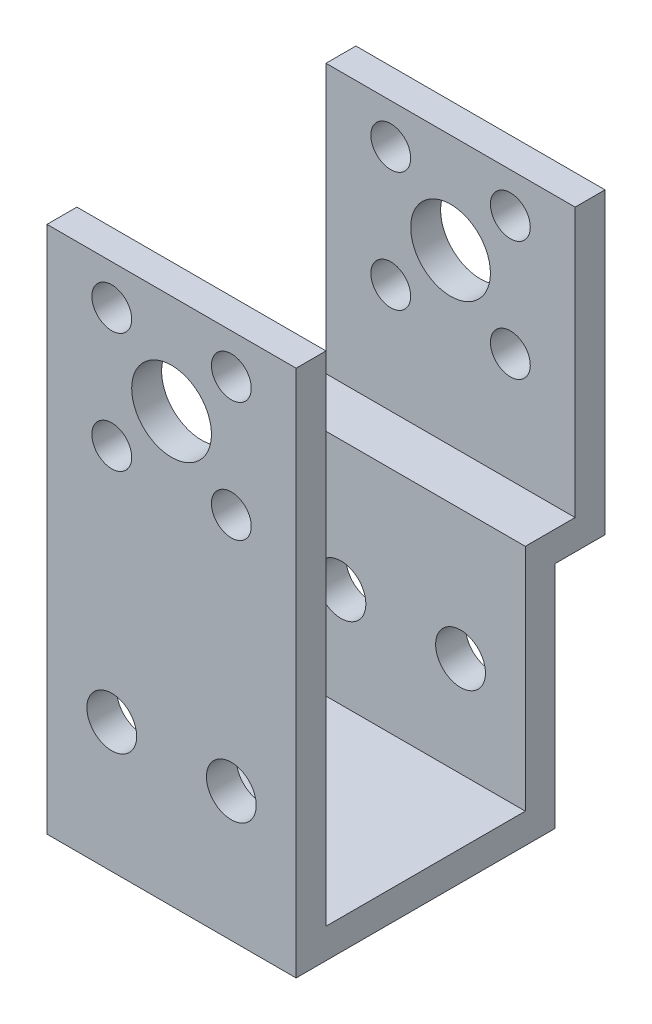
SolidWorks part; units mm, degrees
material "6061 合金"
ref_plane "前视基准面" through (0, 0, 0) normal (0, 0, 1) x (1, 0, 0)
ref_plane "上视基准面" through (0, 0, 0) normal (0, 1, 0) x (1, 0, 0)
ref_plane "右视基准面" through (0, 0, 0) normal (1, 0, 0) x (0, 0, -1)
sketch "草图1" plane through (0, 0, 0) normal (0, 0, 1) x (1, 0, 0)
  line L0 (12.5, 50) -> (12.5, 0) construction
  line L1 (0, 0) -> (25, 0)
  line L2 (0, 0) -> (0, 50)
  line L3 (0, 50) -> (25, 50)
  line L4 (25, 0) -> (25, 50)
  dimension "D5" = 50
  dimension "D7" = 25
extrude "凸台-拉伸1" add sketch "草图1" along normal blind 3
sketch "草图4" plane through (0, 0, 0) normal (-1, 0, 0) x (0, 0, 1)
  line L0 (-23, -3) -> (-23, 20.0181)
  line L1 (3, 0) -> (-20, 0)
  line L2 (3, 0) -> (3, -3)
  line L3 (3, -3) -> (-23, -3)
  line L5 (-23, 20.0181) -> (-28, 20.0181)
  line L6 (-20, 0) -> (-20, 23.0181)
  line L7 (-20, 23.0181) -> (-25, 23.0181)
  line L8 (-25, 23.0181) -> (-25, 50)
  line L9 (-28, 20.0181) -> (-28, 50)
  line L10 (-28, 50) -> (-25, 50)
  point P12 (-25, 45.7486)
  dimension "D1" = 26
  dimension "D2" = 3
  dimension "D3" = 3
  dimension "D4" = 3
  dimension "D5" = 28
  dimension "D6" = 3
  dimension "D7" = 50
extrude "凸台-拉伸2" add sketch "草图4" against normal blind 25
sketch "草图2" plane through (0, 0, 0) normal (0, 0, -1) x (-1, 0, 0)
  line L0 (-12.5, -3.0454) -> (-12.5, 50) construction
  line L1 (-25, -3) -> (0, -3) construction
  line L2 (-25, -3) -> (0, -3) construction
  line L3 (-25, 50) -> (0, 50) construction
  line L8 (-20.0476, 40) -> (3.6668, 40) construction
  circle A0 centre (-18.5, 10) radius 2.5
  circle A2 centre (-6.5, 10) radius 2.5
  circle A3 centre (-12.5, 40) radius 4
  circle A4 centre (-6.5, 46) radius 2
  circle A5 centre (-6.5, 34) radius 2
  circle A8 centre (-18.5, 34) radius 2
  circle A9 centre (-18.5, 46) radius 2
  point P4 (-12.1557, -3.0454)
  point P5 (-12.5, 40)
  point P11 (0, 0)
  point P12 (-12.5782, 49.0749)
  point P13 (-12.5, 50)
  point P20 (-12.5, 43.2109)
  dimension "D3" = 5
  dimension "D4" = 8
  dimension "D7" = 4
  dimension "D1" = 6
  dimension "D2" = 13
  dimension "D5" = 6
  dimension "D6" = 43
  dimension "D8" = 6
extrude "切除-拉伸1" cut sketch "草图2" against normal up to next and the other way up to next
